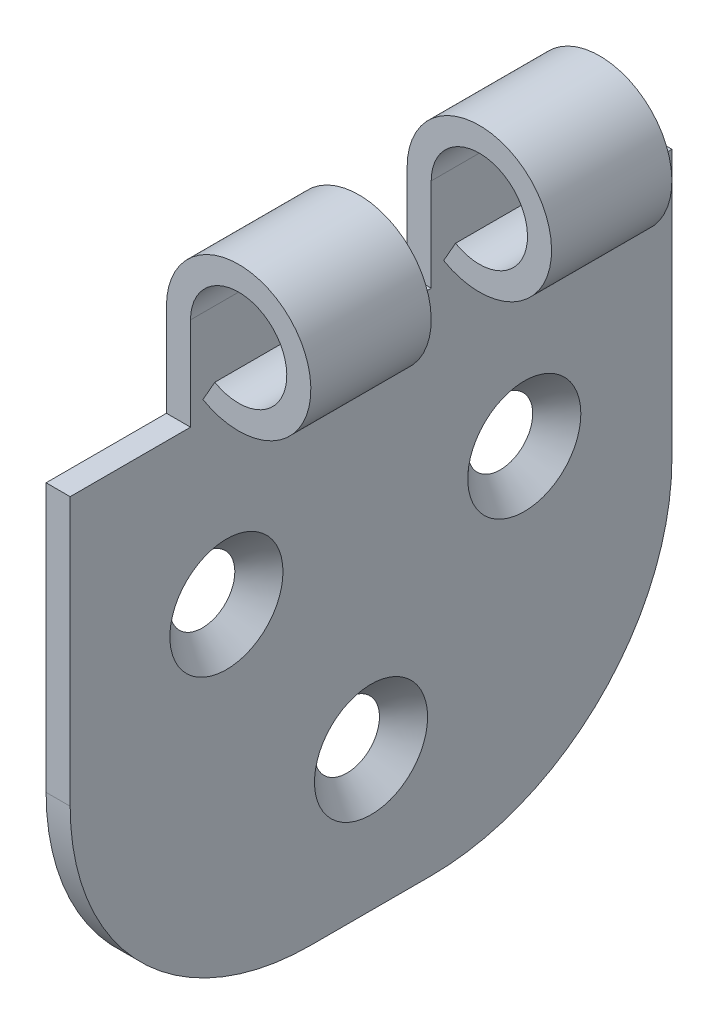
SolidWorks part; units mm, degrees
ref_plane "Front Plane" through (0, 0, 0) normal (0, 0, 1) x (1, 0, 0)
ref_plane "Top Plane" through (0, 0, 0) normal (0, 1, 0) x (1, 0, 0)
ref_plane "Right Plane" through (0, 0, 0) normal (1, 0, 0) x (0, 0, -1)
sketch "Sketch1" plane through (0, 0, 0) normal (0, 0, 1) x (1, 0, 0)
  line L0 (0, 0) -> (0, 50)
  line L1 (0, 50) -> (2, 50) construction
  line L2 (2, 50) -> (2, 0)
  line L3 (2, 0) -> (0, 0)
  line L4 (3.0328, 44.7851) -> (4.0218, 46.5234)
  arc A0 (3.0328, 44.7851) -> (0, 50) centre (6, 50) ccw
  arc A1 (4.0218, 46.5234) -> (2, 50) centre (6, 50) ccw
  dimension "D3" = 12
  dimension "D1" = 50
  dimension "D2" = 2
extrude "Boss-Extrude1" add sketch "Sketch1" along normal mid plane 50
sketch "Sketch2" plane through (2, 0, 0) normal (1, 0, 0) x (0, 0, -1)
  line L0 (-25, 0) -> (-25, 50) construction
  line L14 (-28.1751, 61.0426) -> (-15, 61.0426)
  line L15 (-28.1751, 61.0426) -> (-28.1751, 42.279)
  line L16 (-28.1751, 42.279) -> (-15, 42.279)
  line L17 (-15, 61.0426) -> (-15, 42.279)
  line L18 (-5, 61.0426) -> (5, 61.0426)
  line L19 (-5, 61.0426) -> (-5, 42.279)
  line L20 (-5, 42.279) -> (5, 42.279)
  line L21 (5, 61.0426) -> (5, 42.279)
  line L22 (15, 61.0426) -> (34.623, 61.0426)
  line L23 (15, 61.0426) -> (15, 42.279)
  line L24 (15, 42.279) -> (34.623, 42.279)
  line L25 (34.623, 61.0426) -> (34.623, 42.279)
  dimension "D5" = 10
  dimension "D6" = 10
  dimension "D7" = 10
  dimension "D8" = 10
extrude "Cut-Extrude1" cut sketch "Sketch2" along normal through all both and the other way through all
fillet "Fillet1" radius 20 2 edges at (1, 0, -25) (1, 0, 25)
hole_wizard "CSK for M4 Countersunk Flat Head Screw1" positions "Sketch3" profile "Sketch4" countersink size "M4" standard "ISO" end condition through all
sketch "Sketch3" plane through (2, 0, 0) normal (1, 0, 0) x (0, 0, -1)
  point P0 (0, 11.5875)
  point P2 (-12.0173, 28.0398)
  point P4 (12.7326, 27.0383)
sketch "Sketch4" plane through (2, 11.5875, 0) normal (0, 1, 0) x (0, 0, -1)
  line L0 (0, 0) -> (0, 2)
  line L1 (0, 2) -> (2.25, 2)
  line L2 (2.25, 2) -> (2.25, 2.45)
  line L3 (2.25, 2.45) -> (4.7, 0)
  line L5 (4.7, 0) -> (0, 0)
  line L6 (-2.25, 2.45) -> (-4.7, 0) construction
  line L11 (0, -6.35) -> (0, 107.95) construction
  dimension "Thru Hole Dia." = 4.5
  dimension "Thru Hole Depth" = 2
  dimension "Near C'Sink Dia." = 9.4
  dimension "Near C'Sink Angle" = 90
